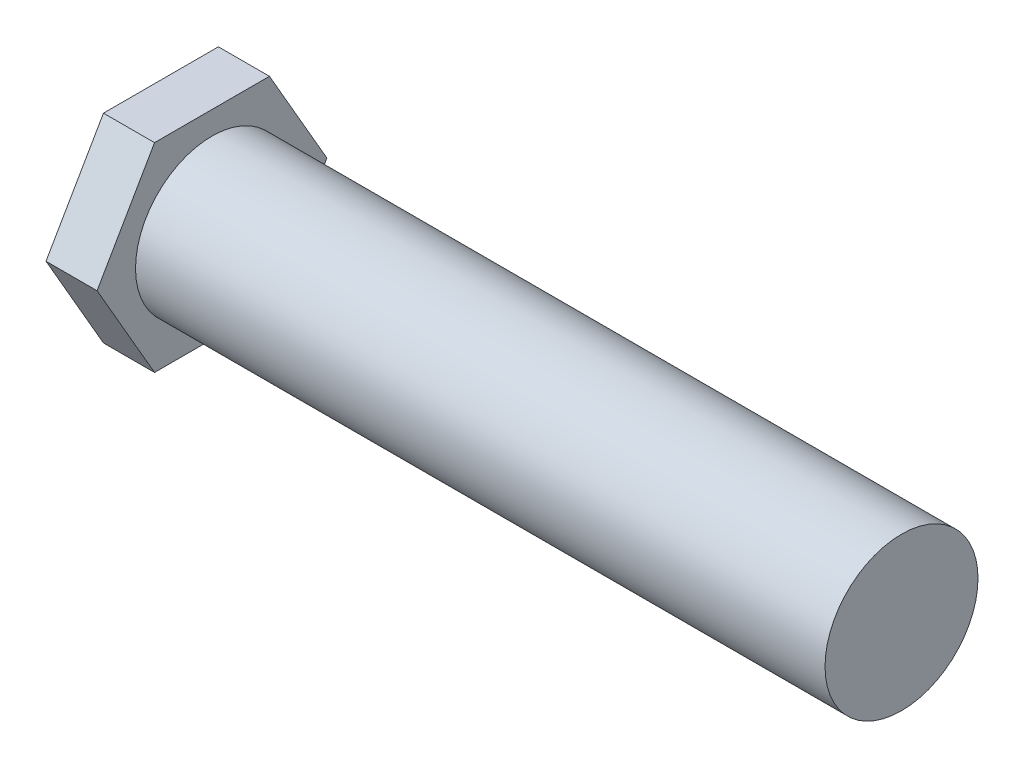
SolidWorks part; units mm, degrees
ref_plane "Front Plane" through (0, 0, 0) normal (0, 0, 1) x (1, 0, 0)
ref_plane "Top Plane" through (0, 0, 0) normal (0, 1, 0) x (1, 0, 0)
ref_plane "Right Plane" through (0, 0, 0) normal (1, 0, 0) x (0, 0, -1)
sketch "Sketch1" plane through (0, 0, 0) normal (1, 0, 0) x (0, 0, -1)
  circle A0 centre (0, 0) radius 29.95
  dimension "D1" = 59.9
extrude "Boss-Extrude1" add sketch "Sketch1" along normal blind 270
sketch "Sketch2" plane through (0, 0, 0) normal (-1, 0, 0) x (0, 0, 1)
  line L1 (45, 0) -> (22.5, 38.9711)
  line L2 (22.5, 38.9711) -> (-22.5, 38.9711)
  line L3 (-22.5, 38.9711) -> (-45, 0)
  line L4 (-45, 0) -> (-22.5, -38.9711)
  line L5 (-22.5, -38.9711) -> (22.5, -38.9711)
  line L6 (22.5, -38.9711) -> (45, 0)
  circle A0 centre (0, 0) radius 38.9711 construction
  dimension "D1" = 90
extrude "Boss-Extrude2" add sketch "Sketch2" along normal blind 20
